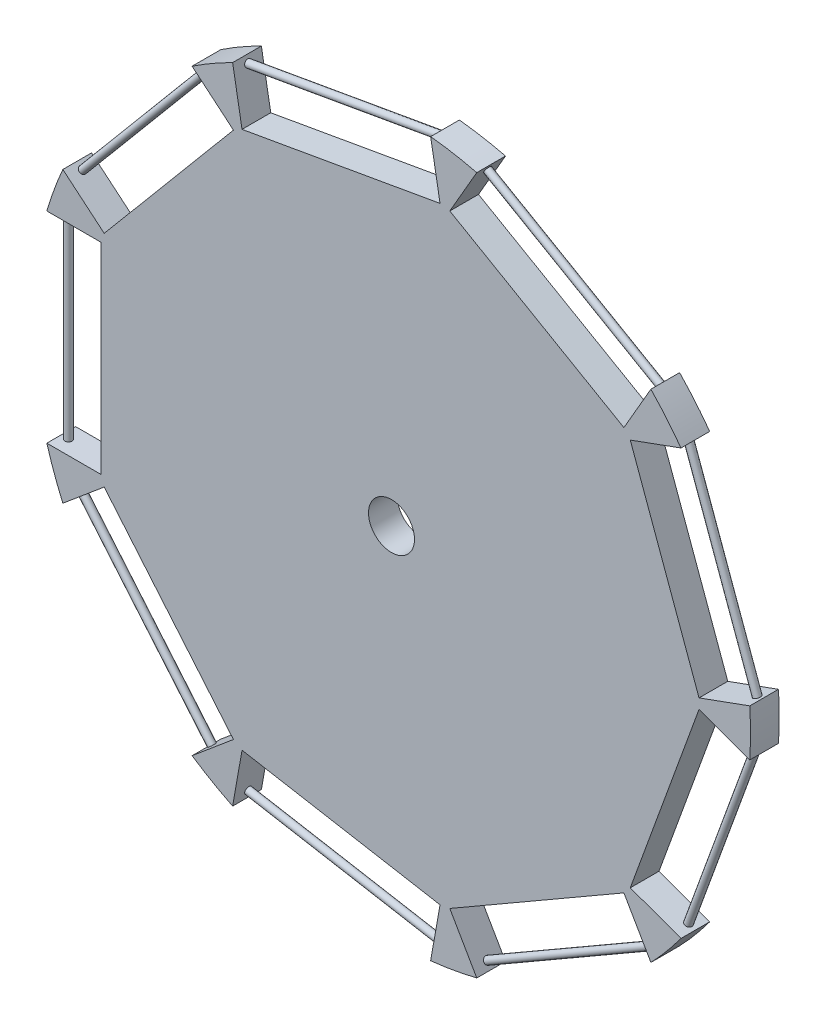
SolidWorks part; units mm, degrees
ref_plane "Front Plane" through (0, 0, 0) normal (0, 0, 1) x (1, 0, 0)
ref_plane "Top Plane" through (0, 0, 0) normal (0, 1, 0) x (1, 0, 0)
ref_plane "Right Plane" through (0, 0, 0) normal (1, 0, 0) x (0, 0, -1)
sketch "Sketch1" plane through (0, 0, 0) normal (0, 0, 1) x (1, 0, 0)
  circle A0 centre (0, 0) radius 50
  dimension "D1" = 100
extrude "Boss-Extrude1" add sketch "Sketch1" along normal blind 4
sketch "Sketch2" plane through (0, 0, 4) normal (0, 0, 1) x (1, 0, 0)
  line L0 (0, 0) -> (50, 0) construction
  line L1 (0, 0) -> (38.3022, 32.1394) construction
  line L2 (0, 0) -> (8.6824, 49.2404) construction
  line L3 (0, 0) -> (-25, 43.3013) construction
  line L4 (0, 0) -> (-46.9846, 17.101) construction
  line L5 (0, 0) -> (-46.9846, -17.101) construction
  line L6 (0, 0) -> (38.3022, -32.1394) construction
  line L7 (0, 0) -> (8.6824, -49.2404) construction
  line L8 (0, 0) -> (-25, -43.3013) construction
  line L9 (38.3022, 32.1394) -> (50, 0) construction
  line L10 (0, 0) -> (44.1511, 16.0697) construction
  line L11 (39.1749, 29.157) -> (33.2548, 27.0023)
  line L12 (33.2548, 27.0023) -> (42.8314, 0.6909)
  line L13 (39.1749, 29.157) -> (48.7515, 2.8456)
  line L14 (42.8314, 0.6909) -> (48.7515, 2.8456)
  line L15 (39.5508, 29.2938) -> (40.317, 29.5727)
  line L16 (39.5508, 29.2938) -> (49.1273, 2.9824)
  line L17 (49.1273, 2.9824) -> (49.8935, 3.2613)
  line L18 (8.6824, 49.2404) -> (38.3022, 32.1394) construction
  line L19 (0, 0) -> (23.4923, 40.6899) construction
  line L20 (11.268, 47.5167) -> (8.118, 42.0607)
  line L21 (8.118, 42.0607) -> (32.3667, 28.0607)
  line L22 (11.268, 47.5167) -> (35.5167, 33.5167)
  line L23 (35.5167, 33.5167) -> (32.3667, 28.0607)
  line L24 (11.468, 47.8631) -> (11.8756, 48.5692)
  line L25 (11.468, 47.8631) -> (35.7167, 33.8631)
  line L26 (35.7167, 33.8631) -> (36.1244, 34.5692)
  line L27 (8.6824, 49.2404) -> (-25, 43.3013) construction
  line L28 (0, 0) -> (-8.1588, 46.2708) construction
  line L29 (-21.9114, 43.6428) -> (-20.8174, 37.4385)
  line L30 (-20.8174, 37.4385) -> (6.7572, 42.3007)
  line L31 (-21.9114, 43.6428) -> (5.6632, 48.5049)
  line L32 (5.6632, 48.5049) -> (6.7572, 42.3007)
  line L33 (-21.9808, 44.0367) -> (-22.1224, 44.8397)
  line L34 (-21.9808, 44.0367) -> (5.5938, 48.8989)
  line L35 (5.5938, 48.8989) -> (5.4522, 49.7018)
  line L36 (-46.9846, 17.101) -> (-25, 43.3013) construction
  line L37 (0, 0) -> (-35.9923, 30.2011) construction
  line L38 (-44.8381, 19.348) -> (-40.0121, 15.2984)
  line L39 (-40.0121, 15.2984) -> (-22.014, 36.7476)
  line L40 (-44.8381, 19.348) -> (-26.8401, 40.7972)
  line L41 (-26.8401, 40.7972) -> (-22.014, 36.7476)
  line L42 (-45.1446, 19.6051) -> (-45.7692, 20.1292)
  line L43 (-45.1446, 19.6051) -> (-27.1465, 41.0543)
  line L44 (-27.1465, 41.0543) -> (-27.7711, 41.5784)
  line L45 (-46.9846, 17.101) -> (-46.9846, -17.101) construction
  line L46 (0, 0) -> (-46.9846, 0) construction
  line L47 (-46.7846, -14) -> (-40.4846, -14)
  line L48 (-40.4846, -14) -> (-40.4846, 14)
  line L49 (-46.7846, -14) -> (-46.7846, 14)
  line L50 (-47.1846, -14) -> (-48, -14)
  line L51 (-47.1846, -14) -> (-47.1846, 14)
  line L52 (-46.7846, 14) -> (-40.4846, 14)
  line L53 (-47.1846, 14) -> (-48, 14)
  line L54 (-46.9846, -17.101) -> (-25, -43.3013) construction
  line L55 (0, 0) -> (-35.9923, -30.2011) construction
  line L56 (-26.8401, -40.7972) -> (-22.014, -36.7476)
  line L57 (-22.014, -36.7476) -> (-40.0121, -15.2984)
  line L58 (-26.8401, -40.7972) -> (-44.8381, -19.348)
  line L59 (-44.8381, -19.348) -> (-40.0121, -15.2984)
  line L60 (-45.1446, -19.6051) -> (-45.7692, -20.1292)
  line L61 (-45.1446, -19.6051) -> (-27.1465, -41.0543)
  line L62 (-27.1465, -41.0543) -> (-27.7711, -41.5784)
  line L63 (8.6824, -49.2404) -> (-25, -43.3013) construction
  line L64 (0, 0) -> (-8.1588, -46.2708) construction
  line L65 (5.6632, -48.5049) -> (6.7572, -42.3007)
  line L66 (6.7572, -42.3007) -> (-20.8174, -37.4385)
  line L67 (5.6632, -48.5049) -> (-21.9114, -43.6428)
  line L68 (-20.8174, -37.4385) -> (-21.9114, -43.6428)
  line L69 (5.5938, -48.8989) -> (5.4522, -49.7018)
  line L70 (5.5938, -48.8989) -> (-21.9808, -44.0367)
  line L71 (-21.9808, -44.0367) -> (-22.1224, -44.8397)
  line L72 (8.6824, -49.2404) -> (38.3022, -32.1394) construction
  line L73 (35.5167, -33.5167) -> (32.3667, -28.0607)
  line L74 (0, 0) -> (23.4923, -40.6899) construction
  line L75 (32.3667, -28.0607) -> (8.118, -42.0607)
  line L76 (35.5167, -33.5167) -> (11.268, -47.5167)
  line L77 (8.118, -42.0607) -> (11.268, -47.5167)
  line L78 (11.468, -47.8631) -> (11.8756, -48.5692)
  line L79 (11.468, -47.8631) -> (35.7167, -33.8631)
  line L80 (35.7167, -33.8631) -> (36.1244, -34.5692)
  line L81 (50, 0) -> (38.3022, -32.1394) construction
  line L82 (0, 0) -> (44.1511, -16.0697) construction
  line L83 (48.7515, -2.8456) -> (42.8314, -0.6909)
  line L84 (48.7515, -2.8456) -> (39.1749, -29.157)
  line L85 (42.8314, -0.6909) -> (33.2548, -27.0023)
  line L86 (33.2548, -27.0023) -> (39.1749, -29.157)
  line L87 (49.1273, -2.9824) -> (49.8935, -3.2613)
  line L88 (49.1273, -2.9824) -> (39.5508, -29.2938)
  line L89 (39.5508, -29.2938) -> (40.317, -29.5727)
  circle A0 centre (0, 0) radius 50 construction
  arc A1 (49.8935, 3.2613) -> (40.317, 29.5727) centre (0, 0) ccw
  arc A2 (36.1244, 34.5692) -> (11.8756, 48.5692) centre (0, 0) ccw
  arc A3 (5.4522, 49.7018) -> (-22.1224, 44.8397) centre (0, 0) ccw
  arc A4 (-27.7711, 41.5784) -> (-45.7692, 20.1292) centre (0, 0) ccw
  arc A5 (-48, 14) -> (-48, -14) centre (0, 0) ccw
  arc A6 (-45.7692, -20.1292) -> (-27.7711, -41.5784) centre (0, 0) ccw
  arc A7 (-25, -43.3013) -> (-24.9979, -43.3025) centre (0, 0) ccw
  arc A8 (-22.1224, -44.8397) -> (5.4522, -49.7018) centre (0, 0) ccw
  arc A9 (11.8756, -48.5692) -> (36.1244, -34.5692) centre (0, 0) ccw
  arc A10 (40.317, -29.5727) -> (49.8935, -3.2613) centre (0, 0) ccw
  circle M1 centre (0, 0) radius 50
  dimension "D1" = 40
  dimension "D2" = 80
  dimension "D3" = 120
  dimension "D4" = 160
  dimension "D5" = 200
  dimension "D6" = 40
  dimension "D7" = 80
  dimension "D8" = 120
  dimension "D9" = 6.3
  dimension "D10" = 90
  dimension "D11" = 6.5
  dimension "D12" = 14
  dimension "D13" = 28
  dimension "D14" = 28
  dimension "D15" = 0.2
  dimension "D16" = 90
  dimension "D17" = 14
  dimension "D18" = 6.3
  dimension "D19" = 6.5
  dimension "D20" = 90
  dimension "D21" = 14
  dimension "D22" = 28
  dimension "D23" = 0.2
  dimension "D24" = 90
  dimension "D25" = 14
  dimension "D26" = 28
  dimension "D27" = 6.3
  dimension "D28" = 6.5
  dimension "D29" = 90
  dimension "D30" = 14
  dimension "D31" = 28
  dimension "D32" = 28
  dimension "D33" = 0.2
  dimension "D34" = 90
  dimension "D35" = 14
  dimension "D36" = 28
  dimension "D37" = 6.3
  dimension "D38" = 90
  dimension "D39" = 14
  dimension "D40" = 6.5
  dimension "D41" = 28
  dimension "D42" = 28
  dimension "D43" = 90
  dimension "D44" = 0.2
  dimension "D45" = 14
  dimension "D46" = 28
  dimension "D47" = 6.3
  dimension "D48" = 6.5
  dimension "D49" = 14
  dimension "D50" = 28
  dimension "D51" = 28
  dimension "D52" = 0.2
  dimension "D53" = 28
  dimension "D54" = 6.3
  dimension "D55" = 6.5
  dimension "D56" = 90
  dimension "D57" = 14
  dimension "D58" = 28
  dimension "D59" = 28
  dimension "D60" = 90
  dimension "D61" = 0.2
  dimension "D62" = 14
  dimension "D63" = 28
  dimension "D64" = 6.3
  dimension "D65" = 6.5
  dimension "D66" = 90
  dimension "D67" = 14
  dimension "D68" = 28
  dimension "D69" = 28
  dimension "D70" = 0.2
  dimension "D71" = 90
  dimension "D72" = 14
  dimension "D73" = 28
  dimension "D74" = 6.3
  dimension "D75" = 90
  dimension "D76" = 6.5
  dimension "D77" = 14
  dimension "D78" = 28
  dimension "D79" = 28
  dimension "D80" = 0.2
  dimension "D81" = 90
  dimension "D82" = 14
  dimension "D83" = 28
  dimension "D84" = 6.3
  dimension "D85" = 6.5
  dimension "D86" = 90
  dimension "D87" = 14
  dimension "D88" = 28
  dimension "D89" = 28
  dimension "D90" = 0.2
  dimension "D91" = 90
  dimension "D92" = 14
  dimension "D93" = 28
extrude "Cut-Extrude1" cut sketch "Sketch2" against normal blind 4 contours L32 L31 L29 L30 | L34 L35 L33 M1 | L23 L22 L20 L21 | L12 L14 L13 L11 | L16 L17 L15 M1 | L88 L89 L87 M1 | L75 L77 L76 L73 | L70 L71 L69 M1 | L66 L68 L67 L65 | L62 L61 L60 M1 | L59 L58 L56 L57 | L51 L53 L50 M1 | L52 L49 L47 L48 | L41 L40 L38 L39 | L43 L44 L42 M1 | A2 L24 L25 L26 | L85 L86 L84 L83 | L79 L80 A9 L78
sketch "Sketch5" plane through (0, 0, 4) normal (0, 0, 1) x (1, 0, 0)
  line L0 (39.1749, 29.157) -> (39.5508, 29.2938)
  line L1 (39.5508, 29.2938) -> (49.1273, 2.9824)
  line L2 (49.1273, 2.9824) -> (48.7515, 2.8456)
  line L3 (48.7515, 2.8456) -> (39.1749, 29.157)
  line L4 (39.1749, -29.157) -> (39.5508, -29.2938)
  line L5 (39.5508, -29.2938) -> (49.1273, -2.9824)
  line L6 (49.1273, -2.9824) -> (48.7515, -2.8456)
  line L7 (48.7515, -2.8456) -> (39.1749, -29.157)
  line L8 (11.268, -47.5167) -> (11.468, -47.8631)
  line L9 (11.468, -47.8631) -> (35.7167, -33.8631)
  line L10 (35.7167, -33.8631) -> (35.5167, -33.5167)
  line L11 (35.5167, -33.5167) -> (11.268, -47.5167)
  line L12 (-21.9114, -43.6428) -> (-21.9808, -44.0367)
  line L13 (-21.9808, -44.0367) -> (5.5938, -48.8989)
  line L14 (5.5938, -48.8989) -> (5.6632, -48.5049)
  line L15 (5.6632, -48.5049) -> (-21.9114, -43.6428)
  line L16 (-27.1465, -41.0543) -> (-26.8401, -40.7972)
  line L17 (-26.8401, -40.7972) -> (-44.8381, -19.348)
  line L18 (-44.8381, -19.348) -> (-45.1446, -19.6051)
  line L19 (-45.1446, -19.6051) -> (-27.1465, -41.0543)
  line L20 (-47.1846, -14) -> (-46.7846, -14)
  line L21 (-46.7846, -14) -> (-46.7846, 14)
  line L22 (-46.7846, 14) -> (-47.1846, 14)
  line L23 (-47.1846, 14) -> (-47.1846, -14)
  line L24 (-45.1446, 19.6051) -> (-44.8381, 19.348)
  line L25 (-44.8381, 19.348) -> (-26.8401, 40.7972)
  line L26 (-26.8401, 40.7972) -> (-27.1465, 41.0543)
  line L27 (-27.1465, 41.0543) -> (-45.1446, 19.6051)
  line L28 (-21.9808, 44.0367) -> (-21.9114, 43.6428)
  line L29 (-21.9114, 43.6428) -> (5.6632, 48.5049)
  line L30 (5.6632, 48.5049) -> (5.5938, 48.8989)
  line L31 (5.5938, 48.8989) -> (-21.9808, 44.0367)
  line L32 (11.268, 47.5167) -> (11.468, 47.8631)
  line L33 (11.468, 47.8631) -> (35.7167, 33.8631)
  line L34 (35.7167, 33.8631) -> (35.5167, 33.5167)
  line L35 (35.5167, 33.5167) -> (11.268, 47.5167)
extrude "Cut-Extrude2" cut sketch "Sketch5" against normal blind 1.8
sketch "Sketch7" plane through (0, 0, 0) normal (0, 0, -1) x (-1, 0, 0)
  line L0 (46.7846, 14) -> (47.1846, 14)
  line L1 (47.1846, 14) -> (47.1846, -14)
  line L2 (47.1846, -14) -> (46.7846, -14)
  line L3 (46.7846, -14) -> (46.7846, 14)
  line L4 (44.8381, -19.348) -> (45.1446, -19.6051)
  line L5 (45.1446, -19.6051) -> (27.1465, -41.0543)
  line L6 (27.1465, -41.0543) -> (26.8401, -40.7972)
  line L7 (26.8401, -40.7972) -> (44.8381, -19.348)
  line L8 (21.9114, -43.6428) -> (21.9808, -44.0367)
  line L9 (21.9808, -44.0367) -> (-5.5938, -48.8989)
  line L10 (-5.5938, -48.8989) -> (-5.6632, -48.5049)
  line L11 (-5.6632, -48.5049) -> (21.9114, -43.6428)
  line L12 (-11.268, -47.5167) -> (-11.468, -47.8631)
  line L13 (-11.468, -47.8631) -> (-35.7167, -33.8631)
  line L14 (-35.7167, -33.8631) -> (-35.5167, -33.5167)
  line L15 (-35.5167, -33.5167) -> (-11.268, -47.5167)
  line L16 (-39.1749, -29.157) -> (-39.5508, -29.2938)
  line L17 (-39.5508, -29.2938) -> (-49.1273, -2.9824)
  line L18 (-49.1273, -2.9824) -> (-48.7515, -2.8456)
  line L19 (-48.7515, -2.8456) -> (-39.1749, -29.157)
  line L20 (-48.7515, 2.8456) -> (-49.1273, 2.9824)
  line L21 (-49.1273, 2.9824) -> (-39.5508, 29.2938)
  line L22 (-39.5508, 29.2938) -> (-39.1749, 29.157)
  line L23 (-39.1749, 29.157) -> (-48.7515, 2.8456)
  line L24 (-35.7167, 33.8631) -> (-11.468, 47.8631)
  line L25 (-11.468, 47.8631) -> (-11.268, 47.5167)
  line L26 (-11.268, 47.5167) -> (-35.5167, 33.5167)
  line L27 (-35.5167, 33.5167) -> (-35.7167, 33.8631)
  line L28 (-5.5938, 48.8989) -> (-5.6632, 48.5049)
  line L29 (-5.6632, 48.5049) -> (21.9114, 43.6428)
  line L30 (21.9114, 43.6428) -> (21.9808, 44.0367)
  line L31 (21.9808, 44.0367) -> (-5.5938, 48.8989)
  line L32 (27.1465, 41.0543) -> (26.8401, 40.7972)
  line L33 (26.8401, 40.7972) -> (44.8381, 19.348)
  line L34 (44.8381, 19.348) -> (45.1446, 19.6051)
  line L35 (45.1446, 19.6051) -> (27.1465, 41.0543)
extrude "Cut-Extrude3" cut sketch "Sketch7" against normal blind 1.8
ref_plane "Plane1" through (-46.9846, 0, 0) normal (-1, 0, 0) x (0, 0, 1)
sketch "Sketch8" plane through (-46.9846, 0, 0) normal (-1, 0, 0) x (0, 0, 1)
  line L0 (2, -14) -> (2.5, -14)
  line L1 (1.8, -14) -> (2.2, -14) construction
  line L2 (0, -14) -> (4, -14) construction
  line L3 (2.5, -14) -> (2.5, 14)
  line L4 (0, 14) -> (4, 14) construction
  line L5 (2.5, 14) -> (2, 14)
  line L6 (2, 14) -> (2, -14)
  dimension "D1" = 0.5
revolve "Revolve1" add sketch "Sketch8" angle 360 about L6
ref_plane "Plane2" through (-35.9923, 30.2011, 0) normal (-0.766, 0.6428, 0) x (0, 0, 1)
sketch "Sketch9" plane through (-35.9923, 30.2011, 0) normal (-0.766, 0.6428, 0) x (0, 0, 1)
  line L0 (2, -14) -> (2.5, -14)
  line L1 (1.8, -14) -> (2.2, -14) construction
  line L2 (0, -14) -> (4, -14) construction
  line L3 (2.5, -14) -> (2.5, 14)
  line L4 (0, 14) -> (4, 14) construction
  line L5 (2.5, 14) -> (2, 14)
  line L6 (2, 14) -> (2, -14)
  dimension "D1" = 0.5
revolve "Revolve2" add sketch "Sketch9" angle 360 about L6
ref_plane "Plane3" through (-8.1588, 46.2708, 0) normal (-0.1736, 0.9848, 0) x (0.9848, 0.1736, 0)
sketch "Sketch10" plane through (-8.1588, 46.2708, 0) normal (-0.1736, 0.9848, 0) x (0.9848, 0.1736, 0)
  line L0 (14, -2) -> (14, -1.5)
  line L1 (14, 0) -> (14, -4) construction
  line L2 (14, 0) -> (14, -4) construction
  line L3 (14, -1.5) -> (-14, -1.5)
  line L4 (-14, 0) -> (-14, -4) construction
  line L5 (-14, -1.5) -> (-14, -2)
  line L6 (-14, -2) -> (14, -2)
  dimension "D1" = 0.5
revolve "Revolve3" add sketch "Sketch10" angle 360 about L6
ref_plane "Plane4" through (23.4923, 40.6899, 0) normal (0.5, 0.866, 0) x (0.866, -0.5, 0)
sketch "Sketch11" plane through (23.4923, 40.6899, 0) normal (0.5, 0.866, 0) x (0.866, -0.5, 0)
  line L0 (14, -2) -> (14, -1.5)
  line L1 (14, -1.8) -> (14, -2.2) construction
  line L2 (14, 0) -> (14, -4) construction
  line L3 (14, -1.5) -> (-14, -1.5)
  line L4 (-14, 0) -> (-14, -4) construction
  line L5 (-14, -1.5) -> (-14, -2)
  line L6 (-14, -2) -> (14, -2)
  dimension "D1" = 0.5
revolve "Revolve4" add sketch "Sketch11" angle 360 about L6
ref_plane "Plane5" through (44.1511, 16.0697, 0) normal (0.9397, 0.342, 0) x (0, 0, -1)
sketch "Sketch12" plane through (44.1511, 16.0697, 0) normal (0.9397, 0.342, 0) x (0, 0, -1)
  line L0 (-2, -14) -> (-1.5, -14)
  line L1 (-1.8, -14) -> (-2.2, -14) construction
  line L2 (0, -14) -> (-4, -14) construction
  line L3 (-1.5, -14) -> (-1.5, 14)
  line L4 (0, 14) -> (-4, 14) construction
  line L5 (-1.5, 14) -> (-2, 14)
  line L6 (-2, 14) -> (-2, -14)
  dimension "D1" = 0.5
revolve "Revolve5" add sketch "Sketch12" angle 360 about L6
ref_plane "Plane6" through (44.1511, -16.0697, 0) normal (0.9397, -0.342, 0) x (0, 0, -1)
sketch "Sketch13" plane through (44.1511, -16.0697, 0) normal (0.9397, -0.342, 0) x (0, 0, -1)
  line L0 (-2, -14) -> (-1.5, -14)
  line L1 (-1.8, -14) -> (-2.2, -14) construction
  line L2 (0, -14) -> (-4, -14) construction
  line L3 (-1.5, -14) -> (-1.5, 14)
  line L4 (0, 14) -> (-4, 14) construction
  line L5 (-1.5, 14) -> (-2, 14)
  line L6 (-2, 14) -> (-2, -14)
  dimension "D1" = 0.5
revolve "Revolve6" add sketch "Sketch13" angle 360 about L6
ref_plane "Plane7" through (23.4923, -40.6899, 0) normal (0.5, -0.866, 0) x (-0.866, -0.5, 0)
sketch "Sketch14" plane through (23.4923, -40.6899, 0) normal (0.5, -0.866, 0) x (-0.866, -0.5, 0)
  line L0 (-14, -2) -> (-14, -2.5)
  line L1 (-14, -1.8) -> (-14, -2.2) construction
  line L2 (-14, 0) -> (-14, -4) construction
  line L3 (-14, -2.5) -> (14, -2.5)
  line L4 (14, 0) -> (14, -4) construction
  line L5 (14, -2.5) -> (14, -2)
  line L6 (14, -2) -> (-14, -2)
  dimension "D1" = 0.5
revolve "Revolve7" add sketch "Sketch14" angle 360 about L6
ref_plane "Plane8" through (-35.9923, -30.2011, 0) normal (-0.766, -0.6428, 0) x (0, 0, 1)
sketch "Sketch15" plane through (-35.9923, -30.2011, 0) normal (-0.766, -0.6428, 0) x (0, 0, 1)
  line L0 (2, -14) -> (2.5, -14)
  line L1 (1.8, -14) -> (2.2, -14) construction
  line L2 (0, -14) -> (4, -14) construction
  line L3 (2.5, -14) -> (2.5, 14)
  line L4 (0, 14) -> (4, 14) construction
  line L5 (2.5, 14) -> (2, 14)
  line L6 (0, 14) -> (4, 14) construction
  line L7 (2, 14) -> (2, -14)
  dimension "D1" = 0.5
revolve "Revolve8" add sketch "Sketch15" angle 360 about L7
ref_plane "Plane9" through (-8.1588, -46.2708, 0) normal (-0.1736, -0.9848, 0) x (-0.9848, 0.1736, 0)
sketch "Sketch16" plane through (-8.1588, -46.2708, 0) normal (-0.1736, -0.9848, 0) x (-0.9848, 0.1736, 0)
  line L0 (14, -2) -> (14, -1.5)
  line L1 (14, -1.8) -> (14, -2.2) construction
  line L2 (14, 0) -> (14, -4) construction
  line L3 (14, -1.5) -> (-14, -1.5)
  line L4 (-14, 0) -> (-14, -4) construction
  line L5 (-14, -1.5) -> (-14, -2)
  line L6 (-14, -2) -> (14, -2)
  dimension "D1" = 0.5
revolve "Revolve9" add sketch "Sketch16" angle 360 about L6
sketch "Sketch17" plane through (0, 0, 0) normal (0, 0, -1) x (-1, 0, 0)
  circle A0 centre (0, 0) radius 3.2
  dimension "D1" = 6.4
extrude "Cut-Extrude4" cut sketch "Sketch17" against normal blind 10
